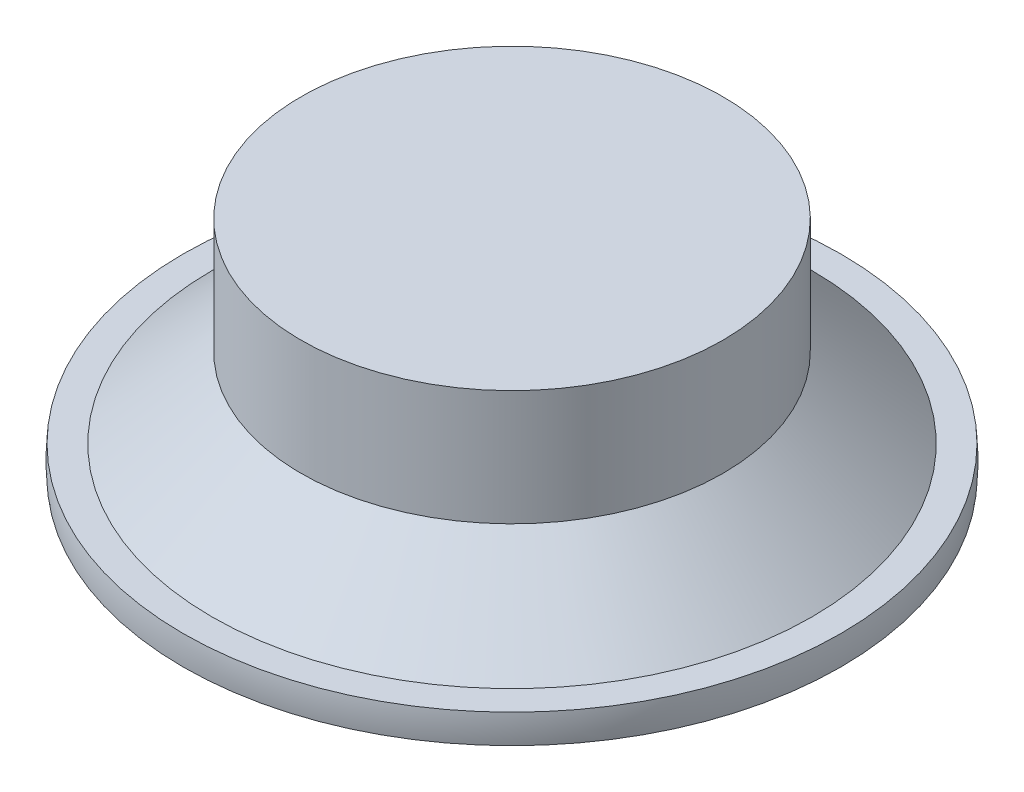
SolidWorks part; units mm, degrees
ref_plane "Plan de face" through (0, 0, 0) normal (0, 0, 1) x (1, 0, 0)
ref_plane "Plan de dessus" through (0, 0, 0) normal (0, 1, 0) x (1, 0, 0)
ref_plane "Plan de droite" through (0, 0, 0) normal (1, 0, 0) x (0, 0, -1)
sketch "Esquisse1" plane through (0, 0, 0) normal (0, 0, 1) x (1, 0, 0)
  line L0 (0, 21.4094) -> (0, 27.2)
  line L1 (0, -43.0328) -> (0, 43.0328) construction
  line L2 (0, 27.2) -> (25.6, 27.2)
  line L3 (25.6, 27.2) -> (25.6, 13.2)
  line L4 (39.9054, 3.52) -> (36.4054, 3.52)
  line L5 (36.4054, 3.52) -> (25.6, 13.2)
  line L6 (22, 0) -> (-22, 0) construction
  line L7 (39.9054, 0) -> (0, 0)
  line L8 (0, 0) -> (0, 27.2)
  line L9 (40, 1.76) -> (40, 0) construction
  line L10 (40, 0) -> (40, -1.4062) construction
  line L11 (0, 27.2) -> (0, 0)
  arc A0 (39.9054, 0) -> (39.9054, 3.52) centre (23.5754, 1.76) ccw
  dimension "D1" = 27.2
  dimension "D2" = 40
  dimension "D3" = 25.6
  dimension "D4" = 3.52
  dimension "D5" = 14
  dimension "D6" = 3.5
revolve "Révolution2" add sketch "Esquisse1" angle 360 about L8
